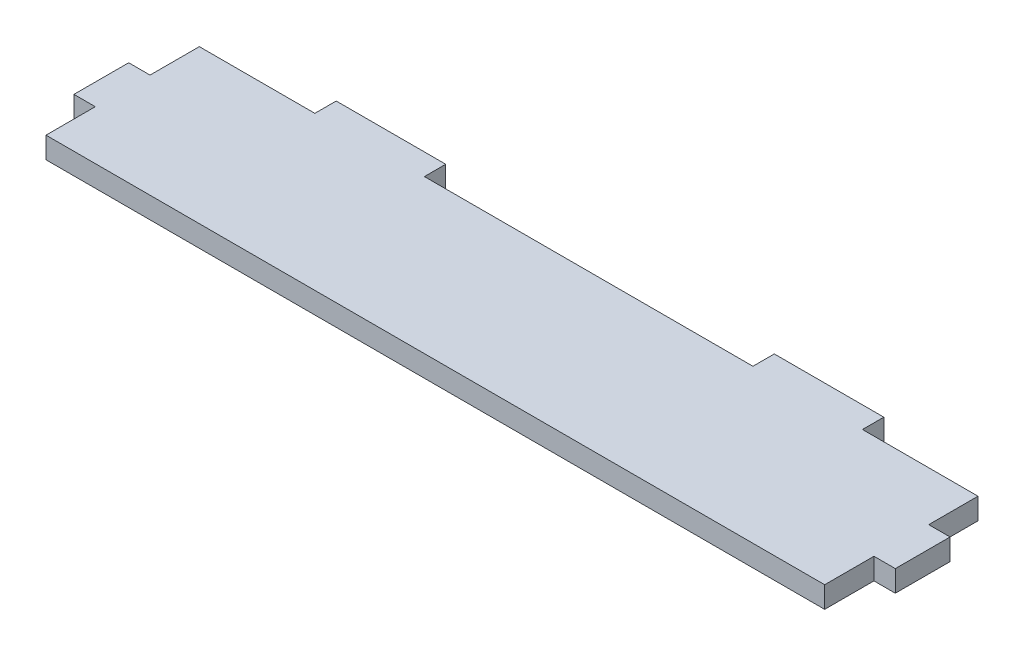
SolidWorks part; units mm, degrees
material "Very Low Density PE (SS)"
ref_plane "Front Plane" through (0, 0, 0) normal (0, 0, 1) x (1, 0, 0)
ref_plane "Top Plane" through (0, 0, 0) normal (0, 1, 0) x (1, 0, 0)
ref_plane "Right Plane" through (0, 0, 0) normal (1, 0, 0) x (0, 0, -1)
sketch "Sketch1" plane through (0, 0, 0) normal (0, 1, 0) x (1, 0, 0)
  line L0 (0, 14) -> (0, -14) construction
  line L1 (-71.1, 14) -> (-50, 14)
  line L2 (-71.1, 14) -> (-71.1, 5)
  line L3 (-71.1, -14) -> (71.1, -14)
  line L4 (71.1, 14) -> (71.1, 5)
  line L5 (-71.1, 14) -> (71.1, -14) construction
  line L6 (-71.1, -14) -> (71.1, 14) construction
  line L7 (-50, 14) -> (-30, 14) construction
  line L8 (-50, 14) -> (-50, 17.9)
  line L9 (-50, 17.9) -> (-30, 17.9)
  line L10 (-30, 14) -> (-30, 17.9)
  line L11 (50, 17.9) -> (30, 17.9)
  line L12 (30, 14) -> (30, 17.9)
  line L13 (50, 14) -> (30, 14) construction
  line L14 (50, 14) -> (50, 17.9)
  line L15 (-50, 14) -> (-30, 14) construction
  line L16 (-30, 14) -> (30, 14)
  line L17 (30, 14) -> (50, 14) construction
  line L18 (50, 14) -> (71.1, 14)
  line L19 (75, -5) -> (71.1, -5)
  line L20 (-75, 5) -> (-71.1, 5)
  line L21 (-75, 5) -> (-75, -5)
  line L22 (-75, -5) -> (-71.1, -5)
  line L23 (-71.1, 5) -> (-71.1, -5) construction
  line L24 (-75, 5) -> (-71.1, -5) construction
  line L25 (-75, -5) -> (-71.1, 5) construction
  line L26 (71.1, 5) -> (71.1, -5) construction
  line L27 (75, 5) -> (71.1, 5)
  line L28 (75, 5) -> (75, -5)
  line L29 (-71.1, 5) -> (-71.1, -5) construction
  line L30 (-71.1, -5) -> (-71.1, -14)
  line L31 (71.1, 5) -> (71.1, -5) construction
  line L32 (71.1, -5) -> (71.1, -14)
  point P0 (0, 0)
  point P17 (-73.05, 0)
  dimension "D1" = 150
  dimension "D2" = 28
  dimension "D3" = 3.9
  dimension "D4" = 21.1
  dimension "D5" = 20
  dimension "D6" = 3.9
  dimension "D7" = 10
extrude "Boss-Extrude1" add sketch "Sketch1" along normal blind 3.9
